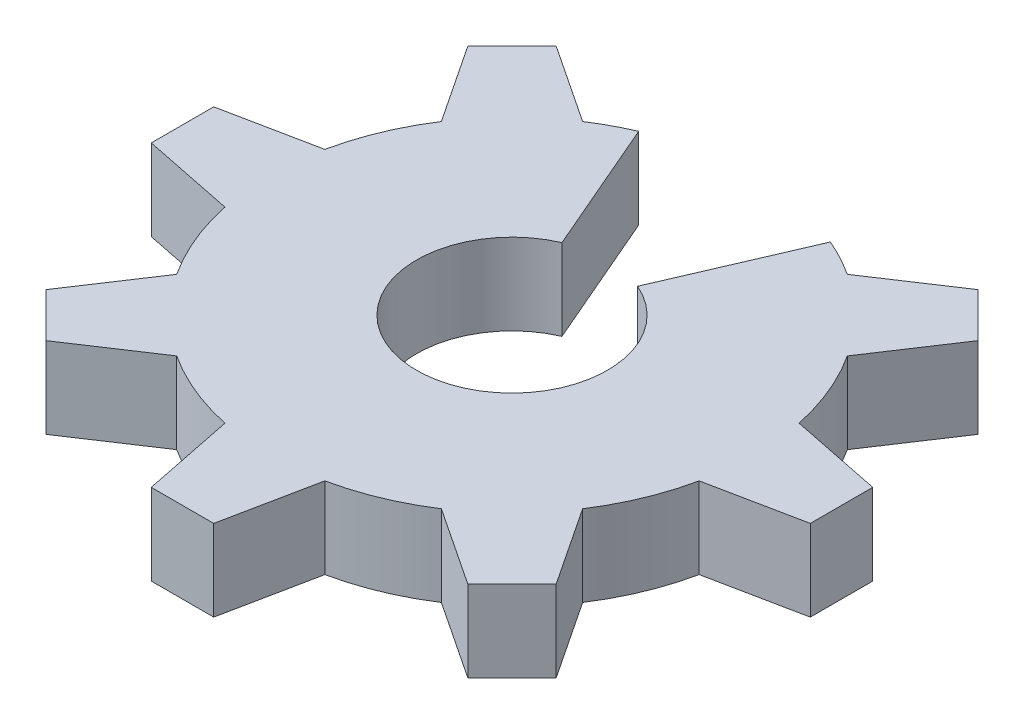
SolidWorks part; units mm, degrees
ref_plane "Front Plane" through (0, 0, 0) normal (0, 0, 1) x (1, 0, 0)
ref_plane "Top Plane" through (0, 0, 0) normal (0, 1, 0) x (1, 0, 0)
ref_plane "Right Plane" through (0, 0, 0) normal (1, 0, 0) x (0, 0, -1)
sketch "Sketch20" plane through (0, 0, -30) normal (0, 1, 0) x (-1, 0, 0)
  line L0 (-42.1209, 45.64) -> (38.9014, 45.64) construction
  line L1 (0, 37.3075) -> (0, -12.7546) construction
  line L2 (-10.1837, 69.2863) -> (9.6012, 23.3464) construction
  line L3 (1.5347, 42.0764) -> (0.6052, 44.2348)
  line L4 (0, 45.64) -> (3.7477, 49.3877) construction
  line L5 (0, 45.64) -> (3.7477, 41.8923) construction
  line L6 (0, 50.9164) -> (0.5, 50.9164)
  line L7 (3.3774, 49.7245) -> (3.731, 49.371)
  line L8 (3.731, 49.371) -> (4.0845, 49.0174)
  line L9 (5.2764, 46.14) -> (5.2764, 45.64)
  line L10 (5.2764, 45.64) -> (5.2764, 45.14)
  line L11 (4.0845, 42.2626) -> (3.731, 41.909)
  line L12 (3.731, 41.909) -> (3.3774, 41.5555)
  line L13 (0.5, 50.9164) -> (0.8, 49.4366)
  line L14 (2.1189, 48.8903) -> (3.3774, 49.7245)
  line L15 (4.0845, 49.0174) -> (3.2503, 47.7589)
  line L16 (5.2764, 46.14) -> (3.7966, 46.44)
  line L17 (5.2764, 45.14) -> (3.7966, 44.84)
  line L18 (4.0845, 42.2626) -> (3.2503, 43.5211)
  line L19 (3.3774, 41.5555) -> (2.1189, 42.3897)
  line L20 (0, 50.9164) -> (-0.5, 50.9164)
  line L21 (-0.5, 50.9164) -> (-0.8, 49.4366)
  line L24 (-2.1189, 48.8903) -> (-3.3774, 49.7245)
  line L25 (-3.3774, 49.7245) -> (-3.731, 49.371)
  line L26 (-3.731, 49.371) -> (-4.0845, 49.0174)
  line L27 (-4.0845, 49.0174) -> (-3.2503, 47.7589)
  line L28 (-3.7966, 46.44) -> (-5.2764, 46.14)
  line L29 (-5.2764, 46.14) -> (-5.2764, 45.64)
  line L30 (-5.2764, 45.64) -> (-5.2764, 45.14)
  line L31 (-5.2764, 45.14) -> (-3.7966, 44.84)
  line L32 (-3.2503, 43.5211) -> (-4.0845, 42.2626)
  line L33 (-4.0845, 42.2626) -> (-3.731, 41.909)
  line L34 (-3.731, 41.909) -> (-3.3774, 41.5555)
  line L35 (-3.3774, 41.5555) -> (-2.1189, 42.3897)
  line L36 (-1.5347, 42.0764) -> (-0.6052, 44.2348)
  circle A0 centre (0, 45.64) radius 1.53 construction
  circle A1 centre (0, 45.64) radius 3.88 construction
  circle A2 centre (0, 45.64) radius 5.3 construction
  arc A3 (-2.1189, 42.3897) -> (-1.5347, 42.0764) centre (0, 45.64) ccw
  arc A4 (1.5347, 42.0764) -> (2.1189, 42.3897) centre (0, 45.64) ccw
  arc A5 (3.2503, 43.5211) -> (3.7966, 44.84) centre (0, 45.64) ccw
  arc A6 (3.7966, 46.44) -> (3.2503, 47.7589) centre (0, 45.64) ccw
  arc A7 (2.1189, 48.8903) -> (0.8, 49.4366) centre (0, 45.64) ccw
  arc A8 (-0.8, 49.4366) -> (-2.1189, 48.8903) centre (0, 45.64) ccw
  arc A9 (-3.2503, 47.7589) -> (-3.7966, 46.44) centre (0, 45.64) ccw
  arc A10 (-3.7966, 44.84) -> (-3.2503, 43.5211) centre (0, 45.64) ccw
  arc A11 (0.6052, 44.2348) -> (-0.6052, 44.2348) centre (0, 45.64) ccw
  dimension "D2" = 3.06
  dimension "D3" = 7.76
  dimension "D5" = 10.6
  dimension "D1" = 15.64
  dimension "D4" = 23.3
  dimension "D6" = 45
  dimension "D7" = 90
  dimension "D8" = 0.5
  dimension "D9" = 0.3
extrude "Boss-Extrude6" add sketch "Sketch20" along normal blind 1.3
